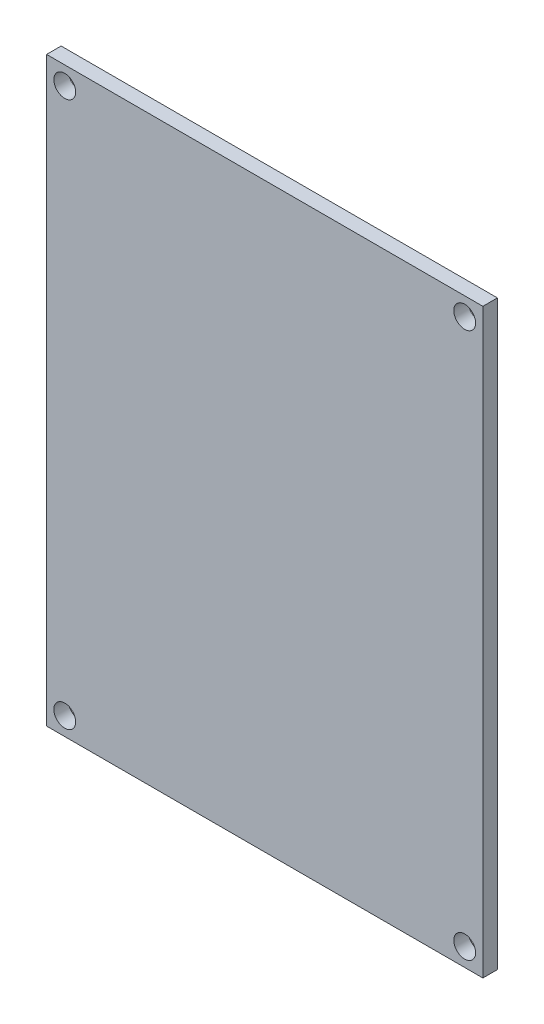
SolidWorks part; units mm, degrees
ref_plane "Alzado" through (0, 0, 0) normal (0, 0, 1) x (1, 0, 0)
ref_plane "Planta" through (0, 0, 0) normal (0, 1, 0) x (1, 0, 0)
ref_plane "Vista lateral" through (0, 0, 0) normal (1, 0, 0) x (0, 0, -1)
sketch "Croquis1" plane through (0, 0, 0) normal (0, 0, 1) x (1, 0, 0)
  line L1 (30, -40) -> (-30, -40)
  line L2 (30, -40) -> (30, 40)
  line L3 (30, 40) -> (-30, 40)
  line L4 (-30, -40) -> (-30, 40)
  line L5 (30, -40) -> (-30, 40) construction
  line L6 (30, 40) -> (-30, -40) construction
  point P0 (0, 0)
  dimension "D1" = 80
  dimension "D2" = 60
extrude "Saliente-Extruir1" add sketch "Croquis1" along normal blind 2
sketch "Croquis2" plane through (0, 0, 0) normal (0, 0, -1) x (-1, 0, 0)
  circle A0 centre (27.5, -37.5) radius 1.5
  circle A1 centre (-27.5, -37.5) radius 1.5
  circle A2 centre (-27.5, 37.5) radius 1.5
  circle A3 centre (27.5, 37.5) radius 1.5
extrude "Cortar-Extruir1" cut sketch "Croquis2" against normal up to next
